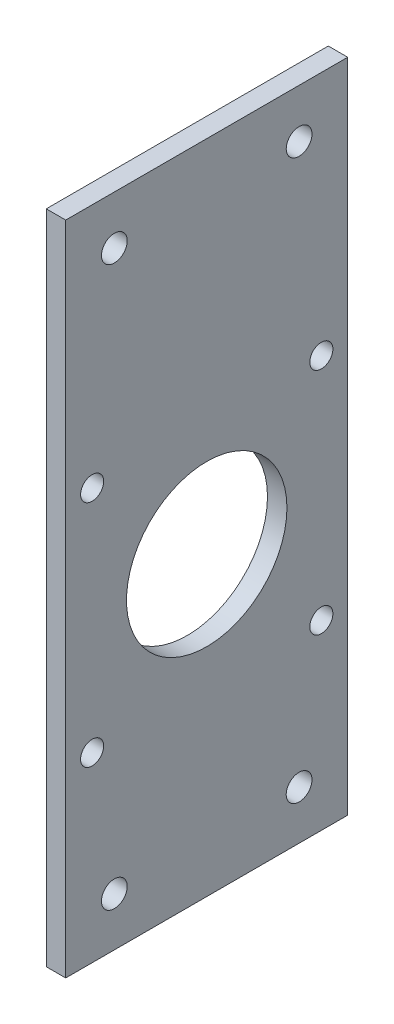
SolidWorks part; units mm, degrees
ref_plane "Front Plane" through (0, 0, 0) normal (0, 0, 1) x (1, 0, 0)
ref_plane "Top Plane" through (0, 0, 0) normal (0, 1, 0) x (1, 0, 0)
ref_plane "Right Plane" through (0, 0, 0) normal (1, 0, 0) x (0, 0, -1)
sketch "Sketch1" plane through (0, 0, 0) normal (1, 0, 0) x (0, 0, -1)
  line L0 (0, 0) -> (0, 61.7868) construction
  line L1 (29, -67.5) -> (-29, -67.5)
  line L2 (29, -67.5) -> (29, 67.5)
  line L3 (29, 67.5) -> (-29, 67.5)
  line L4 (-29, -67.5) -> (-29, 67.5)
  line L5 (29, -67.5) -> (-29, 67.5) construction
  line L6 (29, 67.5) -> (-29, -67.5) construction
  line L7 (0, -6.5) -> (-82.1437, -6.5) construction
  line L8 (29, 0) -> (71.314, 0) construction
  circle A0 centre (0, -6.5) radius 16.5
  circle A1 centre (23.57, 17.07) radius 2.375
  circle A2 centre (-23.57, 17.07) radius 2.375
  circle A3 centre (-23.57, -30.07) radius 2.375
  circle A4 centre (23.57, -30.07) radius 2.375
  circle A5 centre (-19, 57.5) radius 2.65
  circle A7 centre (19, 57.5) radius 2.65
  circle A8 centre (-19, -57.5) radius 2.65
  circle A9 centre (19, -57.5) radius 2.65
  point P0 (0, 0)
  dimension "D3" = 61
  dimension "D6" = 4.75
  dimension "D7" = 10
  dimension "D8" = 5.3
  dimension "D1" = 135
  dimension "D2" = 58
  dimension "D4" = 23.57
  dimension "D5" = 23.57
  dimension "D9" = 10
extrude "Boss-Extrude1" add sketch "Sketch1" along normal blind 4
